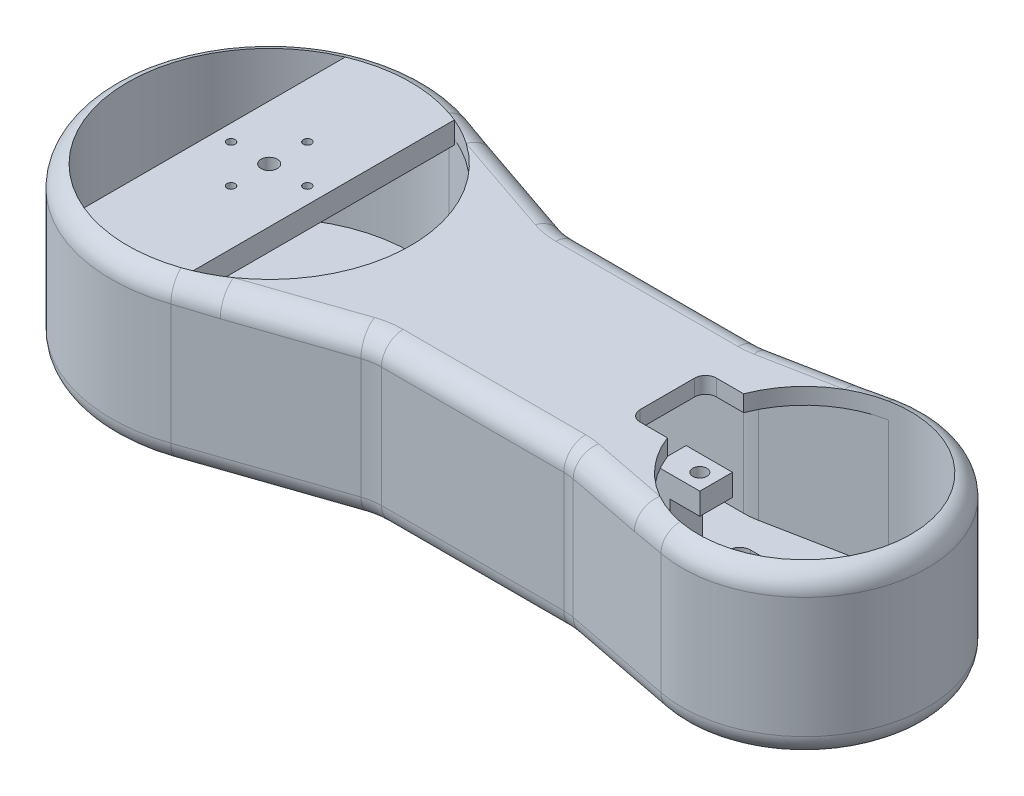
SolidWorks part; units mm, degrees
ref_plane "Front Plane" through (0, 0, 0) normal (0, 0, 1) x (1, 0, 0)
ref_plane "Top Plane" through (0, 0, 0) normal (0, 1, 0) x (1, 0, 0)
ref_plane "Right Plane" through (0, 0, 0) normal (1, 0, 0) x (0, 0, -1)
sketch "Sketch1" plane through (0, 0, 0) normal (0, 1, 0) x (1, 0, 0)
  line L0 (9.3717, 27.4228) -> (35.3717, 18.5373)
  line L1 (38.6056, 18) -> (72.068, 18)
  line L2 (73.9816, 18.1848) -> (93.9816, 22.0842)
  line L3 (8.2873, 0) -> (94.7171, 0) construction
  line L4 (73.9816, -18.1848) -> (93.9816, -22.0842)
  line L5 (38.6056, -18) -> (72.068, -18)
  line L6 (9.3717, -27.4228) -> (35.3717, -18.5373)
  arc A0 (9.3717, 27.4228) -> (9.3717, -27.4228) centre (0, 0) ccw
  arc A1 (93.9816, -22.0842) -> (93.9816, 22.0842) centre (98.2873, 0) ccw
  arc A2 (72.068, 18) -> (73.9816, 18.1848) centre (72.068, 28) ccw
  arc A3 (35.3717, 18.5373) -> (38.6056, 18) centre (38.6056, 28) ccw
  arc A4 (72.068, -18) -> (73.9816, -18.1848) centre (72.068, -28) cw
  arc A5 (35.3717, -18.5373) -> (38.6056, -18) centre (38.6056, -28) cw
  dimension "D1" = 45
  dimension "D2" = 57.96
  dimension "D3" = 10
  dimension "D4" = 90
  dimension "D5" = 18
  dimension "D6" = 20
  dimension "D7" = 26
extrude "Boss-Extrude1" add sketch "Sketch1" along normal blind 30
sketch "Sketch5" plane through (0, 30, 0) normal (0, 1, 0) x (1, 0, 0)
  line L0 (8.4016, -24.584) -> (34.4016, -15.6985)
  line L1 (38.6056, -15) -> (72.068, -15)
  line L2 (74.5557, -15.2403) -> (94.5557, -19.1396)
  line L3 (94.5557, 19.1396) -> (74.5557, 15.2403)
  line L4 (72.068, 15) -> (38.6056, 15)
  line L5 (34.4016, 15.6985) -> (8.4016, 24.584)
  line L6 (9.3717, -27.4228) -> (35.3717, -18.5373)
  line L7 (38.6056, -18) -> (72.068, -18)
  line L8 (73.9816, -18.1848) -> (93.9816, -22.0842)
  line L9 (93.9816, 22.0842) -> (73.9816, 18.1848)
  line L10 (72.068, 18) -> (38.6056, 18)
  line L11 (35.3717, 18.5373) -> (9.3717, 27.4228)
  line L12 (9.3717, -27.4228) -> (35.3717, -18.5373)
  line L13 (38.6056, -18) -> (72.068, -18)
  line L14 (73.9816, -18.1848) -> (93.9816, -22.0842)
  line L15 (93.9816, 22.0842) -> (73.9816, 18.1848)
  line L16 (72.068, 18) -> (38.6056, 18)
  line L17 (35.3717, 18.5373) -> (9.3717, 27.4228)
  arc A0 (8.4016, 24.584) -> (8.4016, -24.584) centre (0, 0) ccw
  arc A1 (38.6056, -15) -> (34.4016, -15.6985) centre (38.6056, -28) ccw
  arc A2 (74.5557, -15.2403) -> (72.068, -15) centre (72.068, -28) ccw
  arc A3 (94.5557, -19.1396) -> (94.5557, 19.1396) centre (98.2873, 0) ccw
  arc A4 (72.068, 15) -> (74.5557, 15.2403) centre (72.068, 28) ccw
  arc A5 (34.4016, 15.6985) -> (38.6056, 15) centre (38.6056, 28) ccw
  arc A6 (9.3717, 27.4228) -> (9.3717, -27.4228) centre (0, 0) ccw
  arc A7 (38.6056, -18) -> (35.3717, -18.5373) centre (38.6056, -28) ccw
  arc A8 (73.9816, -18.1848) -> (72.068, -18) centre (72.068, -28) ccw
  arc A9 (93.9816, -22.0842) -> (93.9816, 22.0842) centre (98.2873, 0) ccw
  arc A10 (72.068, 18) -> (73.9816, 18.1848) centre (72.068, 28) ccw
  arc A11 (35.3717, 18.5373) -> (38.6056, 18) centre (38.6056, 28) ccw
  arc A12 (9.3717, 27.4228) -> (9.3717, -27.4228) centre (0, 0) ccw
  arc A13 (38.6056, -18) -> (35.3717, -18.5373) centre (38.6056, -28) ccw
  arc A14 (73.9816, -18.1848) -> (72.068, -18) centre (72.068, -28) ccw
  arc A15 (93.9816, -22.0842) -> (93.9816, 22.0842) centre (98.2873, 0) ccw
  arc A16 (72.068, 18) -> (73.9816, 18.1848) centre (72.068, 28) ccw
  arc A17 (35.3717, 18.5373) -> (38.6056, 18) centre (38.6056, 28) ccw
  dimension "D1" = 0
  dimension "D2" = 3
extrude "Cut-Extrude3" cut sketch "Sketch5" against normal blind 24 from offset 3 contours A0 L0 A1 L1 A2 L2 A3 L3 A4 L4 A5 L5 offset against normal yes
sketch "Sketch6" plane through (0, 30, 0) normal (0, 1, 0) x (1, 0, 0)
  circle A0 centre (0, 0) radius 25.98
  circle A1 centre (98.2873, 0) radius 19.5
extrude "Cut-Extrude4" cut sketch "Sketch6" against normal blind 9
fillet "Fillet1" radius 4 22 edges at (73.0293, 0, -18.0463) (83.9816, 0, -20.1345) (120.7873, 0, 0) (83.9816, 0, 20.1345) (73.0293, 0, 18.0463) (55.3368, 0, 18) (36.9665, 0, 18.1352) (22.3717, 0, 22.9801) (-28.98, 0, 0) (22.3717, 0, -22.9801) (36.9665, 0, -18.1352) (36.9665, 30, -18.1352) (55.3368, 30, -18) (73.0293, 30, -18.0463) (83.9816, 30, -20.1345) (83.9816, 30, 20.1345) (73.0293, 30, 18.0463) (55.3368, 30, 18) (36.9665, 30, 18.1352) (22.3717, 30, 22.9801) (55.3368, 0, -18) (22.3717, 30, -22.9801)
ref_plane "Plane1" through (0, 30, 0) normal (0, 1, 0) x (1, 0, 0)
sketch "Sketch7" plane through (0, 30, 0) normal (0, 1, 0) x (1, 0, 0)
  line L2 (10, 23.9783) -> (10, -23.9783)
  line L4 (-10, 23.9783) -> (-10, -23.9783)
  arc A0 (8.4016, 24.584) -> (8.4016, -24.584) centre (0, 0) ccw construction
  arc A1 (10, 23.9783) -> (-10, 23.9783) centre (0, 0) ccw
  arc A2 (14.8332, 21.3292) -> (8.4016, 24.584) centre (0, 0) ccw construction
  arc A3 (8.4016, -24.584) -> (14.8332, -21.3292) centre (0, 0) ccw construction
  arc A5 (-10, -23.9783) -> (10, -23.9783) centre (0, 0) ccw
  circle A6 centre (0, 0) radius 10.5
  circle A7 centre (0, 0) radius 1.5
  circle A8 centre (7, 0) radius 0.75
  circle A9 centre (0, 7) radius 0.75
  circle A10 centre (-7, 0) radius 0.75
  circle A11 centre (0, -7) radius 0.75
  point P24 (0, 0)
  point P25 (0, 0)
  dimension "D1" = 1.5
  dimension "D6" = 3
  dimension "D2" = 7
  dimension "D3" = 7
  dimension "D4" = 7
  dimension "D5" = 7
extrude "Boss-Extrude2" add sketch "Sketch7" against normal blind 4 contours L2 A6 L4 A11 A10 A9 A8 A7 | A6 L2 A1 L4 | A6 L4 A5 L2
sketch "Sketch8" plane through (0, 0, 0) normal (0, -1, 0) x (1, 0, 0)
  circle A0 centre (0, 0) radius 5
extrude "Cut-Extrude5" cut sketch "Sketch8" against normal blind 4
ref_plane "Plane2" through (0, 16.5, 0) normal (0, 1, 0) x (1, 0, 0)
sketch "Sketch10" plane through (0, 16.5, 0) normal (0, 1, 0) x (1, 0, 0)
  line L0 (98.2873, 0) -> (106.7373, 0)
  line L1 (117.5552, 3) -> (105.7373, 3)
  line L2 (103.7373, 1) -> (103.7373, -1)
  line L3 (105.7373, -3) -> (117.5552, -3)
  arc A0 (94.5557, -19.1396) -> (94.5557, 19.1396) centre (98.2873, 0) ccw construction
  circle A1 centre (98.2873, 0) radius 19.5
  circle A2 centre (106.7373, 0) radius 1.3
  arc A3 (103.7373, -1) -> (105.7373, -3) centre (105.7373, -1) ccw
  arc A4 (105.7373, 3) -> (103.7373, 1) centre (105.7373, 1) ccw
  point P15 (103.7373, 3)
  dimension "D2" = 3
  dimension "D5" = 2
  dimension "D1" = 8.45
  dimension "D3" = 3
  dimension "D4" = 3
extrude "Boss-Extrude3" add sketch "Sketch10" against normal blind 4
sketch "Sketch11" plane through (0, 16.5, 0) normal (0, 1, 0) x (1, 0, 0)
  line L0 (76.5373, 3) -> (82.0373, 3)
  line L1 (82.0373, 3) -> (82.0373, -3)
  line L2 (82.0373, -3) -> (76.5373, -3)
  line L3 (76.5373, 3) -> (76.5373, -3)
  line L4 (76.5373, -3) -> (73.5373, -3)
  line L5 (73.5373, -3) -> (73.5373, 3)
  line L6 (73.5373, 3) -> (76.5373, 3)
  circle A0 centre (79.0373, 0) radius 1.3
  arc A1 (94.5557, -19.1396) -> (94.5557, 19.1396) centre (98.2873, 0) ccw construction
  arc A2 (94.5557, -19.1396) -> (94.5557, 19.1396) centre (98.2873, 0) ccw
  dimension "D1" = 2.6
  dimension "D2" = 19.25
  dimension "D3" = 3
  dimension "D4" = 3
  dimension "D5" = 3
  dimension "D6" = 5.5
  dimension "D7" = 5.5
extrude "Boss-Extrude4" add sketch "Sketch11" along normal blind 4 separate body contours L0 L3 L2 L1 A0
sketch "Sketch13" plane through (0, 20.5, 0) normal (0, 1, 0) x (1, 0, 0)
  line L0 (76.5373, -3) -> (73.5373, -3)
  line L1 (73.5373, -3) -> (73.5373, 3)
  line L2 (73.5373, 3) -> (76.5373, 3)
  line L4 (82.0373, 3) -> (76.5373, 3)
  line L5 (76.5373, 3) -> (76.5373, -3)
  line L6 (76.5373, -3) -> (82.0373, -3)
  line L7 (82.0373, -3) -> (82.0373, 3)
  line L8 (82.0373, 3) -> (76.5373, 3)
  line L9 (76.5373, 3) -> (76.5373, -3)
  line L10 (76.5373, -3) -> (82.0373, -3)
  line L11 (82.0373, -3) -> (82.0373, 3)
  line M7 (76.5373, 3) -> (76.5373, -3)
  dimension "D1" = 0
extrude "Boss-Extrude5" add sketch "Sketch13" against normal up to surface (17.5 mm away) contours L2 L1 L0 M7 up to face at (0, 3, 5)
sketch "Sketch14" plane through (0, 30, 0) normal (0, 1, 0) x (1, 0, 0)
  line L0 (75.0871, 7) -> (80.0871, 7)
  line L1 (73.0871, 5) -> (73.0871, -5)
  line L2 (75.0871, -7) -> (80.0871, -7)
  arc A0 (88.6966, 16.9784) -> (88.6966, -16.9784) centre (98.2873, 0) ccw construction
  arc A1 (88.6966, 16.9784) -> (88.6966, -16.9784) centre (98.2873, 0) ccw
  circle A2 centre (79.0373, 0) radius 1.3 construction
  circle A3 centre (79.0373, 0) radius 1.3
  arc A4 (73.0871, -5) -> (75.0871, -7) centre (75.0871, -5) ccw
  arc A5 (75.0871, 7) -> (73.0871, 5) centre (75.0871, 5) ccw
  point P12 (73.0871, -7)
  point P15 (73.0871, 7)
  arc M4 (88.6966, -16.9784) -> (88.6966, 16.9784) centre (98.2873, 0) cw
  dimension "D4" = 2
  dimension "D1" = 7
  dimension "D2" = 7
  dimension "D3" = 7
extrude "Cut-Extrude6" cut sketch "Sketch14" against normal blind 4 contours L0 A5 L1 A4 L2 A3 M4 | A1 A3
sketch "Sketch15" plane through (0, 0, 0) normal (0, -1, 0) x (1, 0, 0)
  line L1 (78.5373, -9.8) -> (107.6289, -9.8)
  line L2 (109.6289, -7.8) -> (109.6289, 7.8)
  line L3 (107.6289, 9.8) -> (78.5373, 9.8)
  line L6 (72.068, 14) -> (38.6056, 14) construction
  line L7 (72.068, 14) -> (38.6056, 14)
  line L8 (38.6056, -14) -> (72.068, -14) construction
  line L10 (76.5373, -7.8) -> (76.5373, 7.8)
  arc A1 (107.6289, -9.8) -> (109.6289, -7.8) centre (107.6289, -7.8) ccw
  arc A2 (109.6289, 7.8) -> (107.6289, 9.8) centre (107.6289, 7.8) ccw
  arc A4 (78.5373, -9.8) -> (76.5373, -7.8) centre (78.5373, -7.8) cw
  arc A5 (76.5373, 7.8) -> (78.5373, 9.8) centre (78.5373, 7.8) cw
  dimension "D3" = 2
  dimension "D1" = 4.2
  dimension "D2" = 4.2
extrude "Cut-Extrude10" cut sketch "Sketch15" against normal blind 4 contours A5 L10 A4 L1 A1 L2 A2 L3
